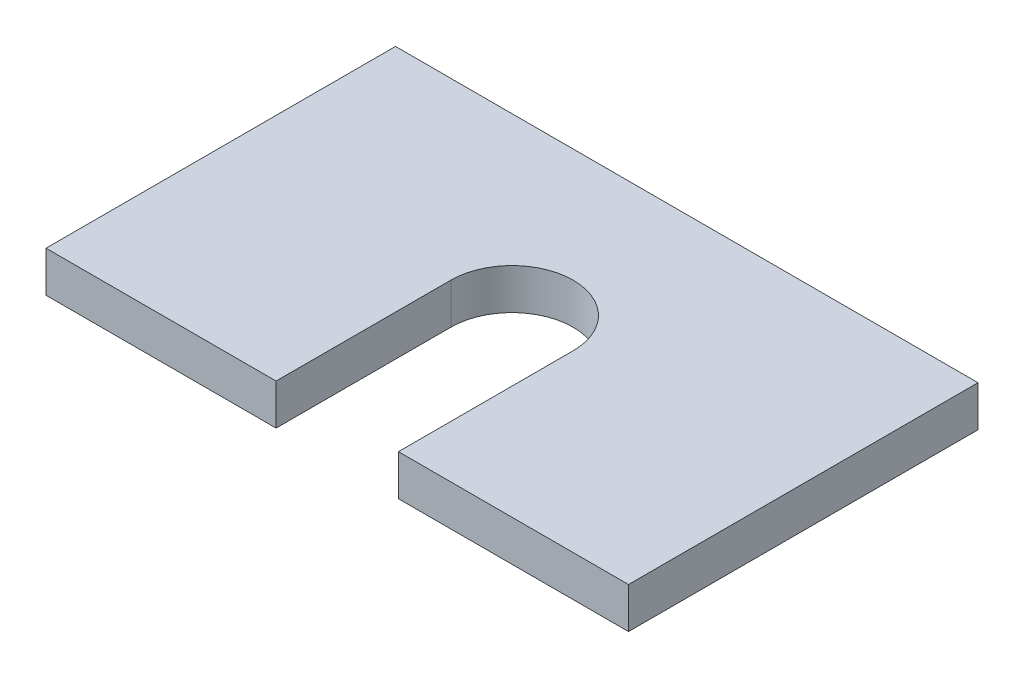
SolidWorks part; units mm, degrees
other "Markup1"
sketch "Sketch3" plane through (-63.5, 8.89, -38.1) normal (-0.9125, 0.4059, -0.0503) x (0.4069, 0.9134, -0.0121)
material "1060 Alloy"
ref_plane "Front Plane" through (0, 0, 0) normal (0, 0, 1) x (1, 0, 0)
ref_plane "Top Plane" through (0, 0, 0) normal (0, 1, 0) x (1, 0, 0)
ref_plane "Right Plane" through (0, 0, 0) normal (1, 0, 0) x (0, 0, -1)
sketch "Sketch1" plane through (0, 0, 0) normal (0, 1, 0) x (1, 0, 0)
  line L0 (-13.335, 0) -> (-13.335, -38.1)
  line L1 (63.5, 38.1) -> (-63.5, 38.1)
  line L2 (63.5, 38.1) -> (63.5, -38.1)
  line L3 (63.5, -38.1) -> (-63.5, -38.1)
  line L4 (-63.5, 38.1) -> (-63.5, -38.1)
  line L5 (63.5, 38.1) -> (-63.5, -38.1) construction
  line L6 (63.5, -38.1) -> (-63.5, 38.1) construction
  line L7 (13.335, 0) -> (13.335, -38.1)
  circle A0 centre (0, 0) radius 13.335
  point P0 (0, 0)
  dimension "D3" = 26.67
  dimension "D1" = 127
  dimension "D2" = 76.2
extrude "Boss-Extrude1" add sketch "Sketch1" along normal blind 8.89 contours A0 L7 L3 L2 L1 L4 L0
